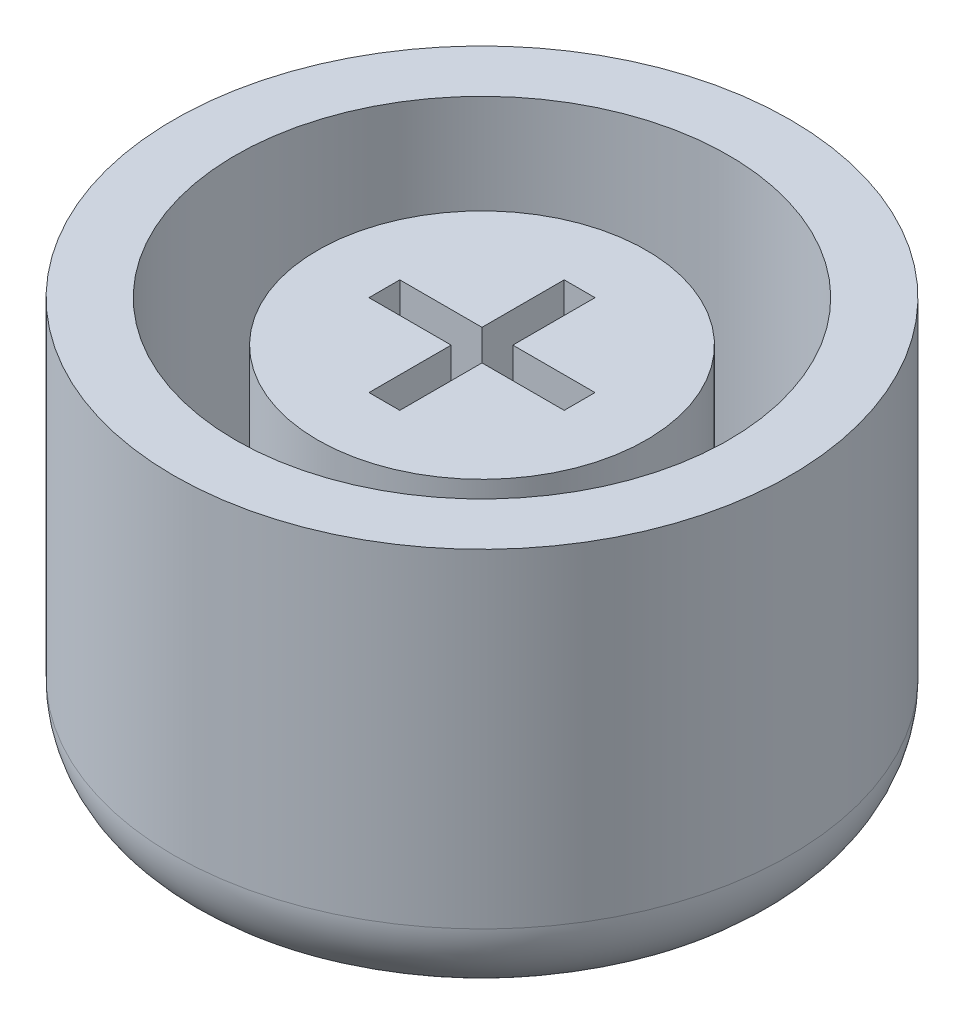
SolidWorks part; units mm, degrees
ref_plane "Front Plane" through (0, 0, 0) normal (0, 0, 1) x (1, 0, 0)
ref_plane "Top Plane" through (0, 0, 0) normal (0, 1, 0) x (1, 0, 0)
ref_plane "Right Plane" through (0, 0, 0) normal (1, 0, 0) x (0, 0, -1)
sketch "Sketch1" plane through (0, 0, 0) normal (0, 1, 0) x (1, 0, 0)
  circle A0 centre (0, 0) radius 7.5
  dimension "D1" = 15
extrude "Boss-Extrude1" add sketch "Sketch1" along normal blind 10
sketch "Sketch2" plane through (0, 10, 0) normal (0, 1, 0) x (1, 0, 0)
  circle A0 centre (0, 0) radius 6
  dimension "D1" = 12
extrude "Cut-Extrude1" cut sketch "Sketch2" against normal blind 8
sketch "Sketch3" plane through (0, 2, 0) normal (0, 1, 0) x (1, 0, 0)
  circle A0 centre (0, 0) radius 4
  dimension "D1" = 8
extrude "Boss-Extrude2" add sketch "Sketch3" along normal blind 7
sketch "Sketch4" plane through (0, 9, 0) normal (0, 1, 0) x (1, 0, 0)
  line L0 (-0.375, 2.375) -> (0.375, 2.375)
  line L1 (0.375, 2.375) -> (0.375, 0.375)
  line L2 (0.375, 0.375) -> (2.375, 0.375)
  line L3 (2.375, 0.375) -> (2.375, -0.375)
  line L4 (2.375, -0.375) -> (0.375, -0.375)
  line L5 (0.375, -0.375) -> (0.375, -2.375)
  line L6 (0.375, -2.375) -> (-0.375, -2.375)
  line L7 (-0.375, -2.375) -> (-0.375, -0.375)
  line L8 (-0.375, -0.375) -> (-2.375, -0.375)
  line L9 (-2.375, -0.375) -> (-2.375, 0.375)
  line L10 (-2.375, 0.375) -> (-0.375, 0.375)
  line L11 (-0.375, 0.375) -> (-0.375, 2.375)
  line L12 (-0.375, -0.375) -> (0.375, 0.375) construction
  point P12 (0, 0)
  dimension "D1" = 0.75
  dimension "D2" = 2
extrude "Cut-Extrude2" cut sketch "Sketch4" against normal blind 7
fillet "Fillet1" radius 2 1 edges at (0, 0, 7.5)
sketch "Sketch5" plane through (0, 0, 0) normal (0, -1, 0) x (1, 0, 0)
  text T0 "C°" font "Century Gothic" height 7
  point P1 (-2.4188, -1.8064)
  point P2 (0, 0)
  point P3 (-2.9852, -2.7556)
  point P4 (-3.4904, -2.5412)
  point P5 (-3.9496, -2.7709)
  point P6 (-4.2099, -3.0311)
  point P7 (-4.6538, -3.1995)
  point P8 (-4.6692, -2.725)
extrude "Cut-Extrude3" cut sketch "Sketch5" against normal blind 1
